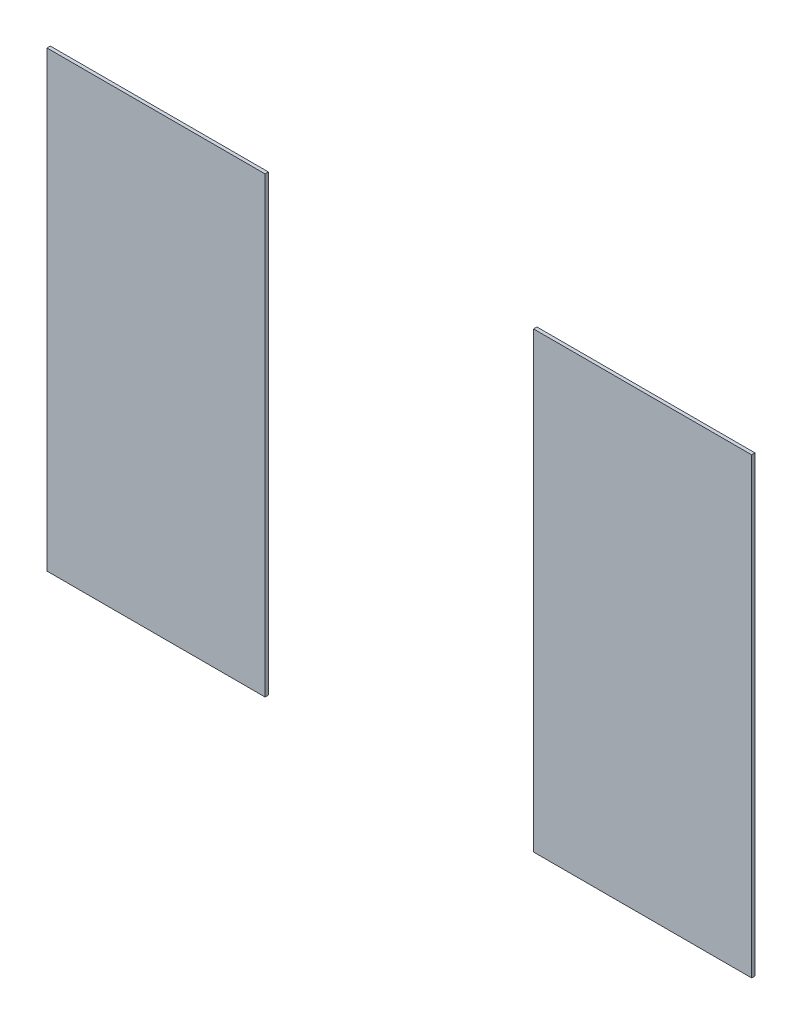
SolidWorks part; units mm, degrees
ref_plane "前视基准面" through (0, 0, 0) normal (0, 0, 1) x (1, 0, 0)
ref_plane "上视基准面" through (0, 0, 0) normal (0, 1, 0) x (1, 0, 0)
ref_plane "右视基准面" through (0, 0, 0) normal (1, 0, 0) x (0, 0, -1)
sketch "草图1" plane through (0, 0, 0) normal (0, 0, 1) x (1, 0, 0)
  line L1 (-2.1, 1.35) -> (-0.8, 1.35)
  line L2 (-2.1, 1.35) -> (-2.1, -1.35)
  line L3 (-2.1, -1.35) -> (-0.8, -1.35)
  line L4 (-0.8, 1.35) -> (-0.8, -1.35)
  line L5 (-2.1, 1.35) -> (-0.8, -1.35) construction
  line L6 (-2.1, -1.35) -> (-0.8, 1.35) construction
  line L7 (0.8, 1.35) -> (2.1, 1.35)
  line L8 (0.8, 1.35) -> (0.8, -1.35)
  line L9 (0.8, -1.35) -> (2.1, -1.35)
  line L10 (2.1, 1.35) -> (2.1, -1.35)
  line L11 (0.8, 1.35) -> (2.1, -1.35) construction
  line L12 (0.8, -1.35) -> (2.1, 1.35) construction
  point P0 (-1.45, 0)
  point P5 (1.45, 0)
  dimension "D1" = 1.35
  dimension "D2" = 1.3
  dimension "D3" = 1.35
  dimension "D4" = 1.3
extrude "凸台-拉伸1" add sketch "草图1" along normal blind 0.02
